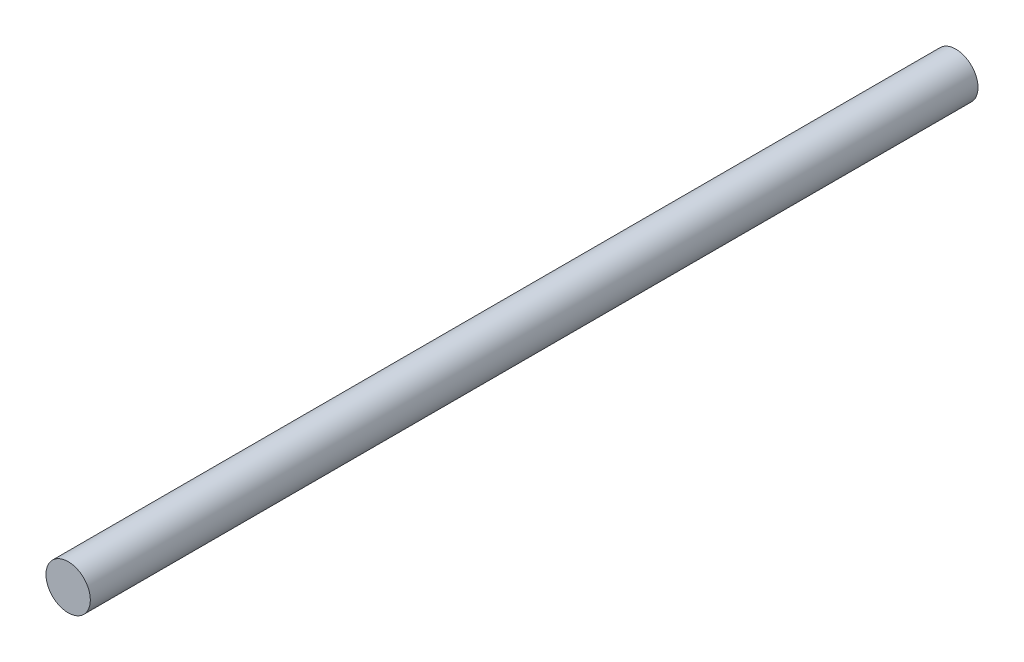
SolidWorks part; units mm, degrees
ref_plane "Front Plane" through (0, 0, 0) normal (0, 0, 1) x (1, 0, 0)
ref_plane "Top Plane" through (0, 0, 0) normal (0, 1, 0) x (1, 0, 0)
ref_plane "Right Plane" through (0, 0, 0) normal (1, 0, 0) x (0, 0, -1)
sketch "Sketch1" plane through (0, 0, 0) normal (0, 0, 1) x (1, 0, 0)
  circle A0 centre (0, 0) radius 10
  dimension "D1" = 20
extrude "Boss-Extrude1" add sketch "Sketch1" along normal blind 400
